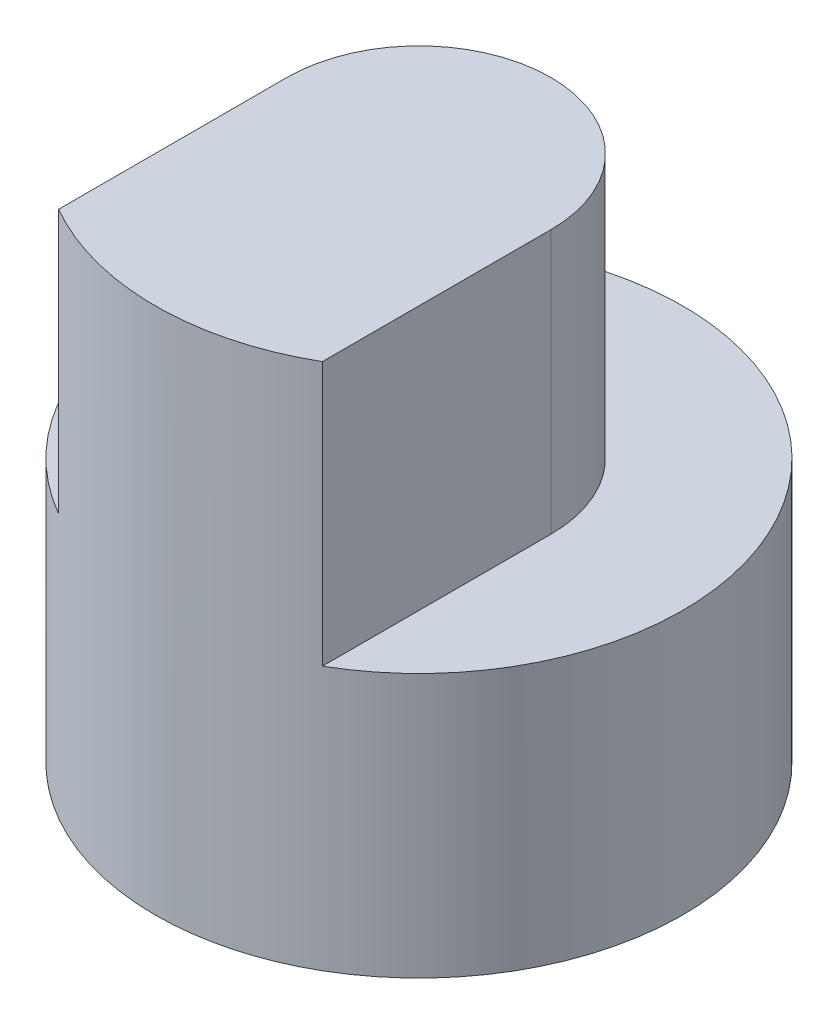
SolidWorks part; units mm, degrees
ref_plane "Front" through (0, 0, 0) normal (0, 0, 1) x (1, 0, 0)
ref_plane "Top" through (0, 0, 0) normal (0, 1, 0) x (1, 0, 0)
ref_plane "Right" through (0, 0, 0) normal (1, 0, 0) x (0, 0, -1)
sketch "Sketch1" plane through (0, 0, 0) normal (0, 1, 0) x (1, 0, 0)
  circle A0 centre (0, 0) radius 2
  dimension "D1" = 4
extrude "Boss-Extrude1" add sketch "Sketch1" along normal blind 2
sketch "Sketch2" plane through (0, 2, 0) normal (0, 1, 0) x (1, 0, 0)
  line L0 (-1, -1.7321) -> (-1, 0)
  line L1 (1, 0) -> (1, -1.7321)
  circle A0 centre (0, 0) radius 2 construction
  arc A1 (-1, 0) -> (1, 0) centre (0, 0) cw
  arc A2 (-1, -1.7321) -> (1, -1.7321) centre (0, 0) ccw
  point P8 (0, 0)
  dimension "D1" = 2
extrude "Boss-Extrude2" add sketch "Sketch2" along normal blind 2
